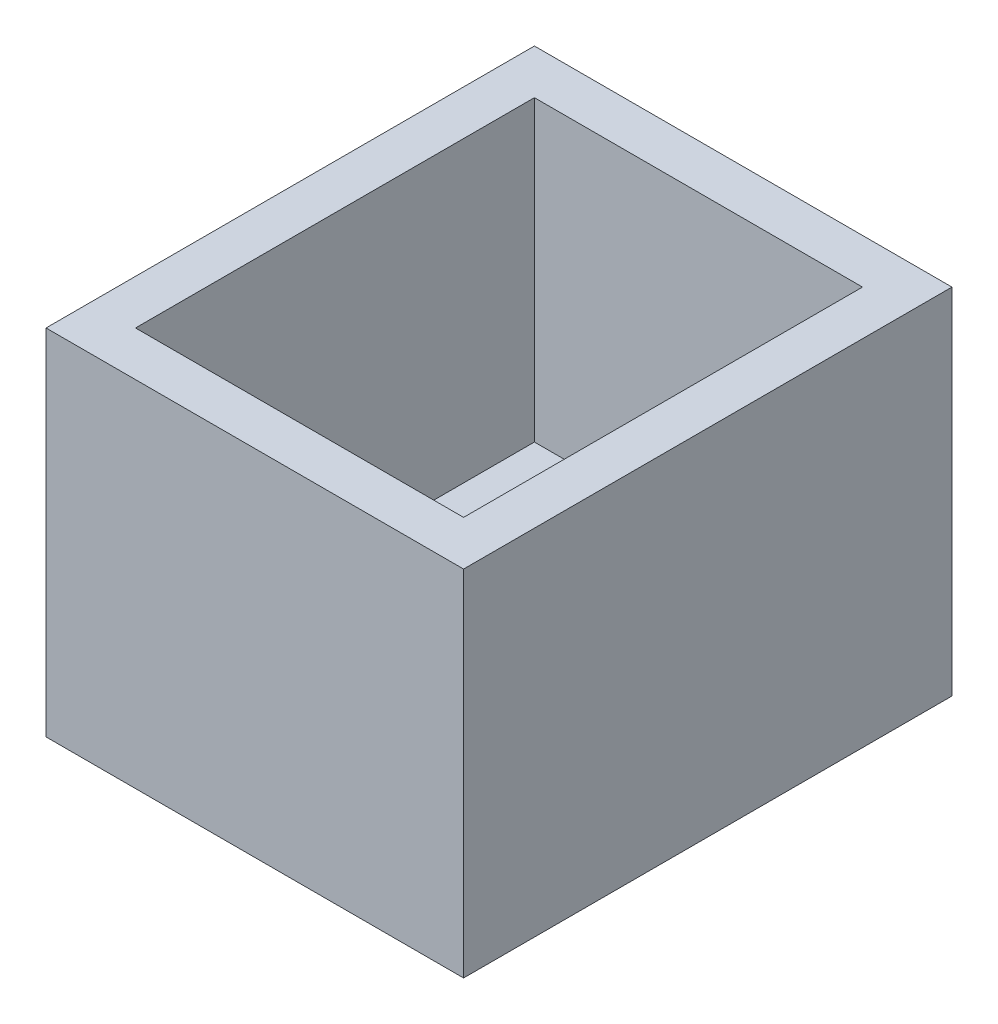
SolidWorks part; units mm, degrees
ref_plane "Front Plane" through (0, 0, 0) normal (0, 0, 1) x (1, 0, 0)
ref_plane "Top Plane" through (0, 0, 0) normal (0, 1, 0) x (1, 0, 0)
ref_plane "Right Plane" through (0, 0, 0) normal (1, 0, 0) x (0, 0, -1)
sketch "Sketch1" plane through (0, 0, 0) normal (0, 1, 0) x (1, 0, 0)
  line L0 (-58.4846, -28.2798) -> (-58.4846, -1.5298)
  line L1 (-55.4846, -25.2798) -> (-39.4846, -25.2798)
  line L2 (-55.4846, -25.2798) -> (-55.4846, -4.5298)
  line L3 (-55.4846, -4.5298) -> (-39.4846, -4.5298)
  line L4 (-39.4846, -25.2798) -> (-39.4846, -4.5298)
  line L5 (-58.4846, -1.5298) -> (-36.4846, -1.5298)
  line L6 (-36.4846, -28.2798) -> (-36.4846, -1.5298)
  line L7 (-58.4846, -28.2798) -> (-36.4846, -28.2798)
  dimension "D1" = 20.75
  dimension "D2" = 16
  dimension "D3" = 3
extrude "Boss-Extrude2" add sketch "Sketch1" along normal blind 3.75
sketch "Sketch2" plane through (0, 3.75, 0) normal (0, 1, 0) x (1, 0, 0)
  line L0 (-39.4846, -4.5298) -> (-55.4846, -4.5298) construction
  line L1 (-55.4846, -25.2798) -> (-39.4846, -25.2798) construction
  line L2 (-50.9846, -25.2798) -> (-55.4846, -25.2798)
  line L3 (-55.4846, -25.2798) -> (-55.4846, -4.5298)
  line L4 (-55.4846, -4.5298) -> (-55.4846, -25.2798) construction
  line L5 (-55.4846, -4.5298) -> (-50.9846, -4.5298)
  line L6 (-43.9846, -4.5298) -> (-39.4846, -4.5298)
  line L7 (-39.4846, -4.5298) -> (-39.4846, -25.2798)
  line L8 (-39.4846, -25.2798) -> (-43.9846, -25.2798)
  line L9 (-50.9846, -24.0298) -> (-54.2346, -24.0298)
  line L10 (-54.2346, -24.0298) -> (-54.2346, -5.7798)
  line L11 (-54.2346, -5.7798) -> (-50.9846, -5.7798)
  line L12 (-43.9846, -5.7798) -> (-40.7346, -5.7798)
  line L13 (-40.7346, -5.7798) -> (-40.7346, -24.0298)
  line L14 (-40.7346, -24.0298) -> (-43.9846, -24.0298)
  line L15 (-50.9846, -5.7798) -> (-50.9846, -4.5298)
  line L16 (-43.9846, -5.7798) -> (-43.9846, -4.5298)
  line L17 (-43.9846, -25.2798) -> (-43.9846, -24.0298)
  line L18 (-50.9846, -25.2798) -> (-50.9846, -24.0298)
  circle A0 centre (-47.4846, -4.5298) radius 3.5 construction
  circle A1 centre (-47.4846, -25.2798) radius 3.5 construction
  dimension "D1" = 7
  dimension "D2" = 7
  dimension "D3" = 1.25
extrude "Boss-Extrude3" add sketch "Sketch2" against normal blind 1.875
sketch "Sketch3" plane through (0, 0, 1.5298) normal (0, 0, -1) x (-1, 0, 0)
  line L1 (58.4846, 0) -> (36.4846, 0)
  line L2 (58.4846, 0) -> (58.4846, 3.75)
  line L3 (58.4846, 3.75) -> (36.4846, 3.75)
  line L4 (36.4846, 0) -> (36.4846, 3.75)
extrude "Boss-Extrude4" add sketch "Sketch3" along normal blind 3
sketch "Sketch4" plane through (-58.4846, 0, 0) normal (-1, 0, 0) x (0, 0, 1)
  line L1 (28.2798, 3.75) -> (-1.4702, 3.75)
  line L2 (28.2798, 3.75) -> (28.2798, 0)
  line L3 (28.2798, 0) -> (-1.4702, 0)
  line L4 (-1.4702, 3.75) -> (-1.4702, 0)
extrude "Boss-Extrude5" add sketch "Sketch4" along normal blind 3
sketch "Sketch5" plane through (0, 0, 28.2798) normal (0, 0, 1) x (1, 0, 0)
  line L1 (-36.4846, 3.75) -> (-61.4846, 3.75)
  line L2 (-36.4846, 3.75) -> (-36.4846, 0)
  line L3 (-36.4846, 0) -> (-61.4846, 0)
  line L4 (-61.4846, 3.75) -> (-61.4846, 0)
extrude "Boss-Extrude6" add sketch "Sketch5" along normal blind 3
sketch "Sketch6" plane through (-36.4846, 0, 0) normal (1, 0, 0) x (0, 0, -1)
  line L0 (1.4702, 3.75) -> (1.4702, 0) construction
  line L1 (1.4702, 3.75) -> (-31.2798, 3.75)
  line L2 (1.4702, 3.75) -> (1.4702, 0)
  line L3 (1.4702, 0) -> (-31.2798, 0)
  line L4 (-31.2798, 3.75) -> (-31.2798, 0)
extrude "Boss-Extrude7" add sketch "Sketch6" along normal blind 3
sketch "Sketch7" plane through (0, 3.75, 0) normal (0, 1, 0) x (1, 0, 0)
  line L0 (-36.4846, -1.5298) -> (-36.4846, -28.2798)
  line L1 (-33.4846, 1.4702) -> (-61.4846, 1.4702)
  line L2 (-33.4846, 1.4702) -> (-33.4846, -31.2798)
  line L3 (-33.4846, -31.2798) -> (-61.4846, -31.2798)
  line L4 (-61.4846, 1.4702) -> (-61.4846, -31.2798)
  line L5 (-36.4846, -28.2798) -> (-58.4846, -28.2798)
  line L6 (-58.4846, -1.5298) -> (-58.4846, -28.2798)
  line L7 (-36.4846, -1.5298) -> (-58.4846, -1.5298)
  dimension "D1" = 3
extrude "Boss-Extrude8" add sketch "Sketch7" along normal blind 20
